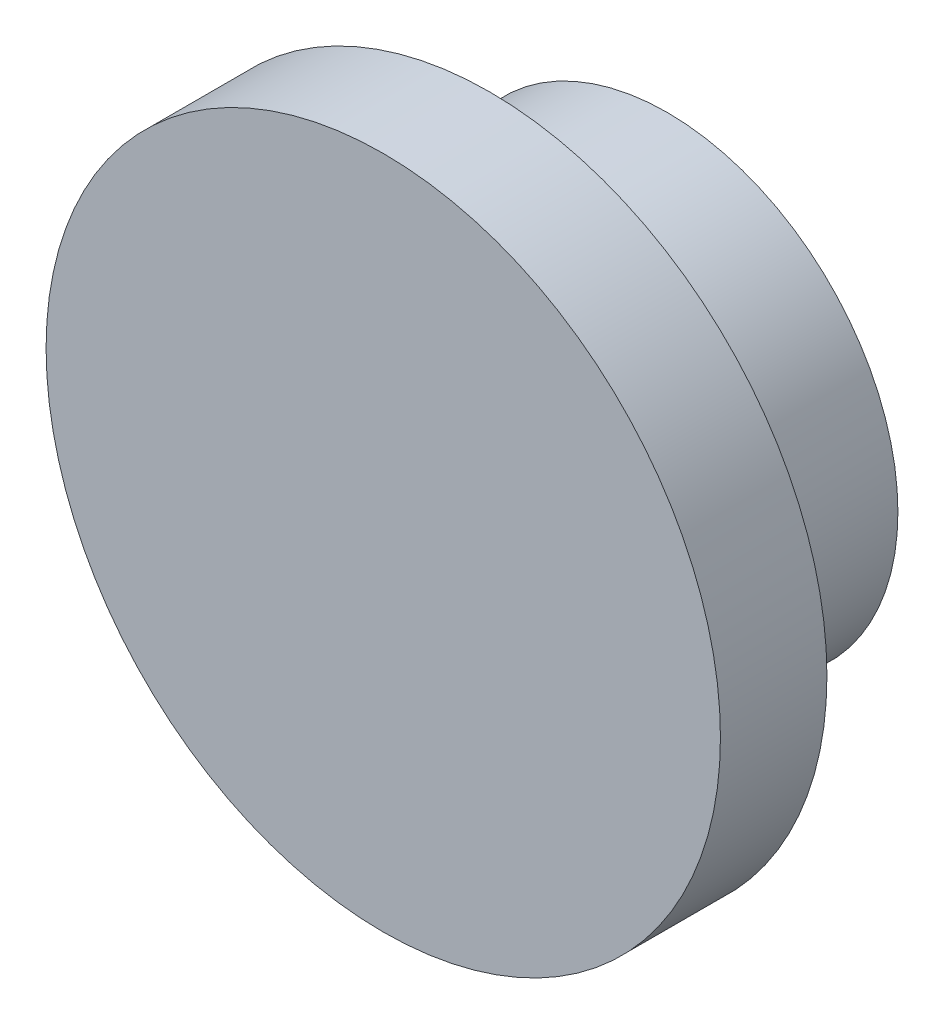
SolidWorks part; units mm, degrees
ref_plane "Front Plane" through (0, 0, 0) normal (0, 0, 1) x (1, 0, 0)
ref_plane "Top Plane" through (0, 0, 0) normal (0, 1, 0) x (1, 0, 0)
ref_plane "Right Plane" through (0, 0, 0) normal (1, 0, 0) x (0, 0, -1)
sketch "Sketch1" plane through (0, 0, 0) normal (1, 0, 0) x (0, 0, -1)
  line L0 (0, 0) -> (0, 2.413)
  line L1 (0, 2.413) -> (0.762, 2.413)
  line L2 (0.762, 2.413) -> (0.762, 1.651)
  line L3 (0.762, 1.651) -> (2.032, 1.651)
  line L4 (2.032, 1.651) -> (2.032, 0)
  line L5 (2.032, 0) -> (0, 0)
  dimension "D1" = 2.413
  dimension "D2" = 0.762
  dimension "D3" = 2.032
  dimension "D4" = 1.27
  dimension "D5" = 1.651
revolve "Revolve1" add sketch "Sketch1" angle 360 about L5
